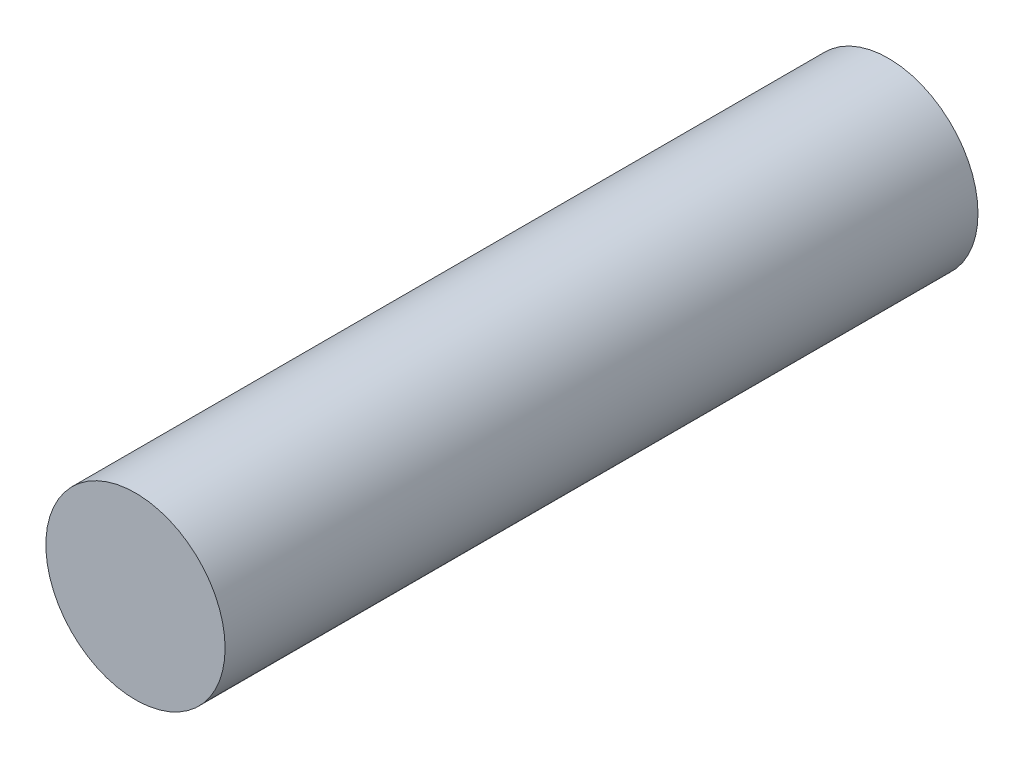
SolidWorks part; units mm, degrees
material "Commercially Pure titanium (Ti-55)  UNS R50550*"
ref_plane "Front Plane" through (0, 0, 0) normal (0, 0, 1) x (1, 0, 0)
ref_plane "Top Plane" through (0, 0, 0) normal (0, 1, 0) x (1, 0, 0)
ref_plane "Right Plane" through (0, 0, 0) normal (1, 0, 0) x (0, 0, -1)
sketch "Sketch1" plane through (0, 0, 0) normal (0, 0, 1) x (1, 0, 0)
  circle A0 centre (0, 0) radius 7.5
  dimension "D1" = 15
extrude "Boss-Extrude1" add sketch "Sketch1" along normal mid plane 63
